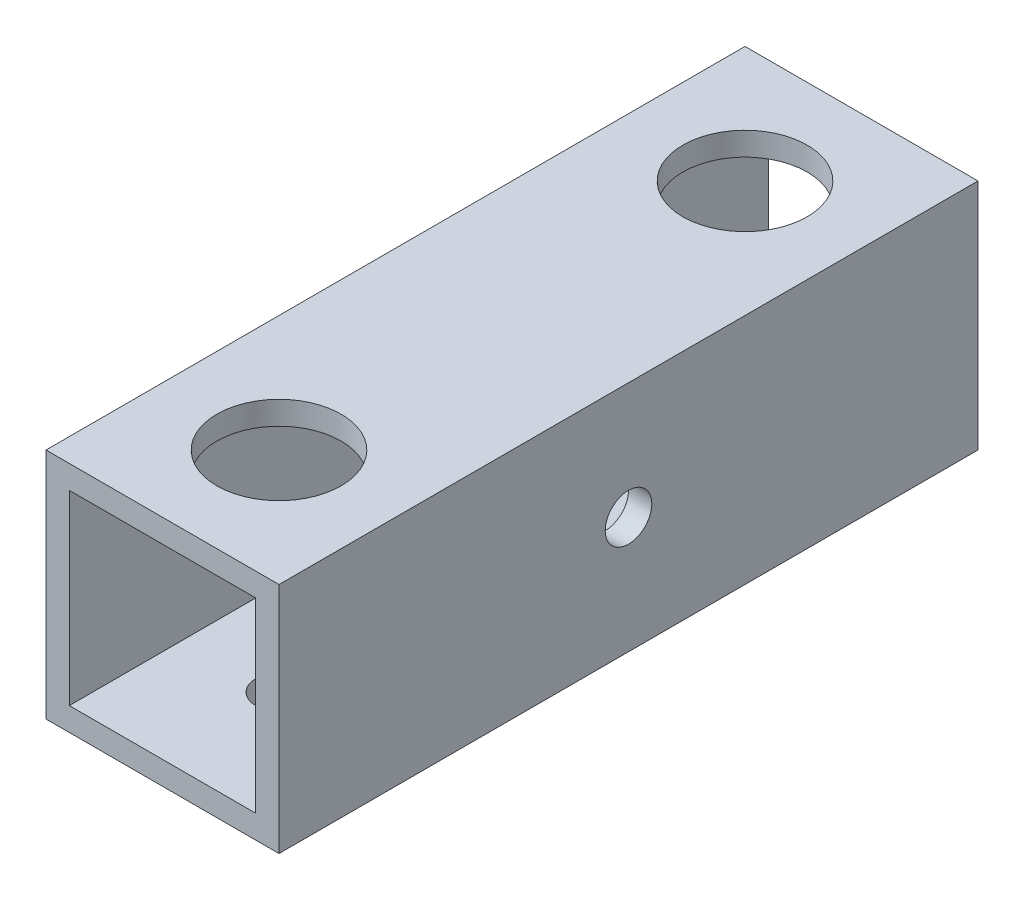
SolidWorks part; units mm, degrees
material "1060 合金"
ref_plane "正面" through (0, 0, 0) normal (0, 0, 1) x (1, 0, 0)
ref_plane "平面" through (0, 0, 0) normal (0, 1, 0) x (1, 0, 0)
ref_plane "右側面" through (0, 0, 0) normal (1, 0, 0) x (0, 0, -1)
sketch "ｽｹｯﾁ1" plane through (0, 0, 0) normal (0, 0, 1) x (1, 0, 0)
  line L1 (-7.0101, 7.7326) -> (7.9899, 7.7326)
  line L2 (-7.0101, 7.7326) -> (-7.0101, -7.2674)
  line L3 (-7.0101, -7.2674) -> (7.9899, -7.2674)
  line L4 (7.9899, 7.7326) -> (7.9899, -7.2674)
  line L9 (-5.5101, 6.2326) -> (6.4899, 6.2326)
  line L10 (-5.5101, 6.2326) -> (-5.5101, -5.7674)
  line L11 (-5.5101, -5.7674) -> (6.4899, -5.7674)
  line L12 (6.4899, 6.2326) -> (6.4899, -5.7674)
  dimension "D1" = 15
  dimension "D2" = 15
  dimension "D3" = 1.5
  dimension "D4" = 1.5
  dimension "D5" = 12
  dimension "D6" = 12
extrude "ﾎﾞｽ - 押し出し2" add sketch "ｽｹｯﾁ1" along normal blind 45
sketch "ｽｹｯﾁ2" plane through (7.9899, 0, 0) normal (1, 0, 0) x (0, 0, -1)
  line L0 (-45, 7.7326) -> (0, 7.7326) construction
  circle A1 centre (-22.5, 0.2326) radius 1.5
  dimension "D1" = 7.5
extrude "ｶｯﾄ - 押し出し1" cut sketch "ｽｹｯﾁ2" against normal blind 10
sketch "ｽｹｯﾁ3" plane through (0, -7.2674, 0) normal (0, -1, 0) x (1, 0, 0)
  line L0 (-7.0101, 0) -> (7.9899, 0) construction
  line L1 (-7.0101, 45) -> (7.9899, 45) construction
  circle A0 centre (0.4899, 37.5) radius 1.5
  circle A1 centre (0.4899, 7.5) radius 1.5
  dimension "D1" = 7.5
  dimension "D2" = 7.5
extrude "ｶｯﾄ - 押し出し2" cut sketch "ｽｹｯﾁ3" against normal blind 10
sketch "ｽｹｯﾁ4" plane through (-7.0101, 0, 0) normal (-1, 0, 0) x (0, 0, 1)
  circle A0 centre (22.5, 0.2326) radius 4
  circle A1 centre (22.5, 0.2326) radius 1.5 construction
  point P2 (0, 0)
extrude "ｶｯﾄ - 押し出し3" cut sketch "ｽｹｯﾁ4" against normal blind 10
sketch "ｽｹｯﾁ5" plane through (0, 7.7326, 0) normal (0, 1, 0) x (1, 0, 0)
  circle A0 centre (0.4899, -7.5) radius 4
  circle A1 centre (0.4899, -37.5) radius 4
  circle A2 centre (0.4899, -37.5) radius 1.5 construction
  circle A3 centre (0.4899, -7.5) radius 1.5 construction
  point P4 (0, 0)
extrude "ｶｯﾄ - 押し出し4" cut sketch "ｽｹｯﾁ5" against normal blind 10
